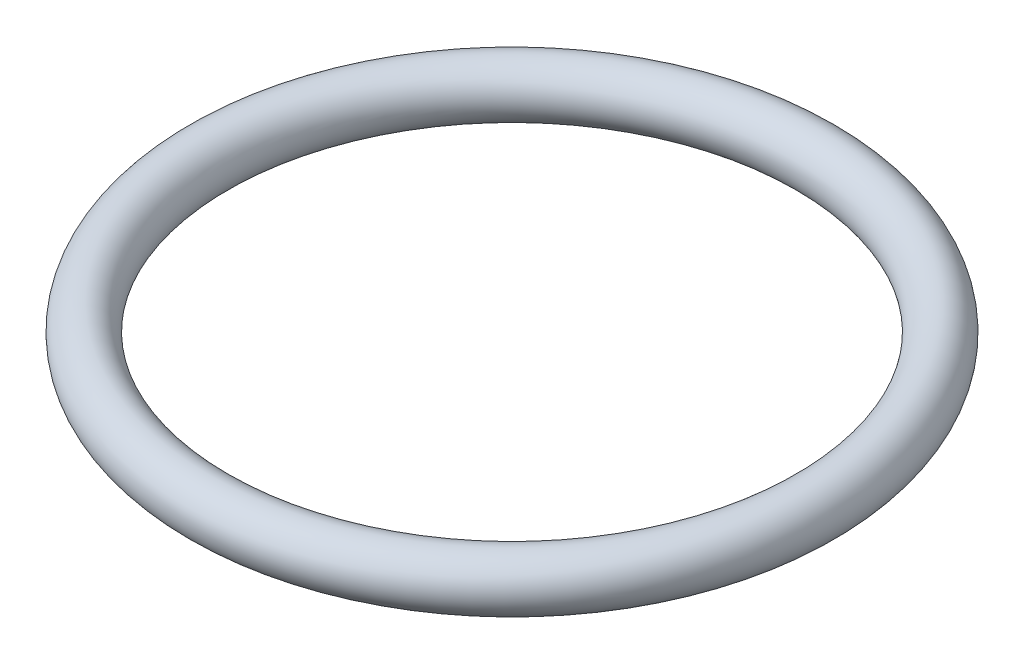
SolidWorks part; units mm, degrees
ref_plane "Front Plane" through (0, 0, 0) normal (0, 0, 1) x (1, 0, 0)
ref_plane "Top Plane" through (0, 0, 0) normal (0, 1, 0) x (1, 0, 0)
ref_plane "Right Plane" through (0, 0, 0) normal (1, 0, 0) x (0, 0, -1)
sketch "Sketch1" plane through (0, 0, 0) normal (0, 0, 1) x (1, 0, 0)
  line L0 (0, 3.1682) -> (0, 0) construction
  line L1 (0, 0) -> (-17, 0) construction
  circle A0 centre (-17, 0) radius 1.5
  dimension "D1" = 3
  dimension "D2" = 17
revolve "Revolve1" add sketch "Sketch1" angle 360 about L0
